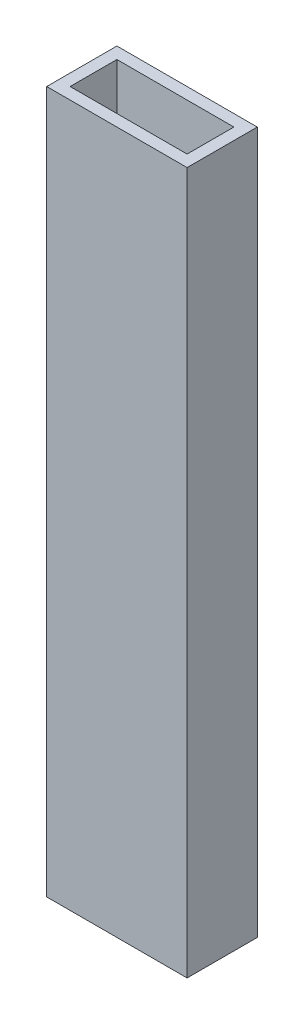
SolidWorks part; units mm, degrees
ref_plane "Front" through (0, 0, 0) normal (0, 0, 1) x (1, 0, 0)
ref_plane "Top" through (0, 0, 0) normal (0, 1, 0) x (1, 0, 0)
ref_plane "Right" through (0, 0, 0) normal (1, 0, 0) x (0, 0, -1)
sketch "Sketch1" plane through (0, 0, 0) normal (0, 1, 0) x (1, 0, 0)
  line L0 (3.175, 3.175) -> (34.925, 3.175)
  line L1 (0, 0) -> (38.1, 0)
  line L2 (0, 0) -> (0, 19.05)
  line L3 (0, 19.05) -> (38.1, 19.05)
  line L4 (38.1, 0) -> (38.1, 19.05)
  line L5 (34.925, 3.175) -> (34.925, 15.875)
  line L6 (3.175, 15.875) -> (34.925, 15.875)
  line L7 (3.175, 3.175) -> (3.175, 15.875)
  dimension "D1" = 38.1
  dimension "D2" = 19.05
  dimension "D3" = 3.175
extrude "Boss-Extrude1" add sketch "Sketch1" along normal blind 190.5
